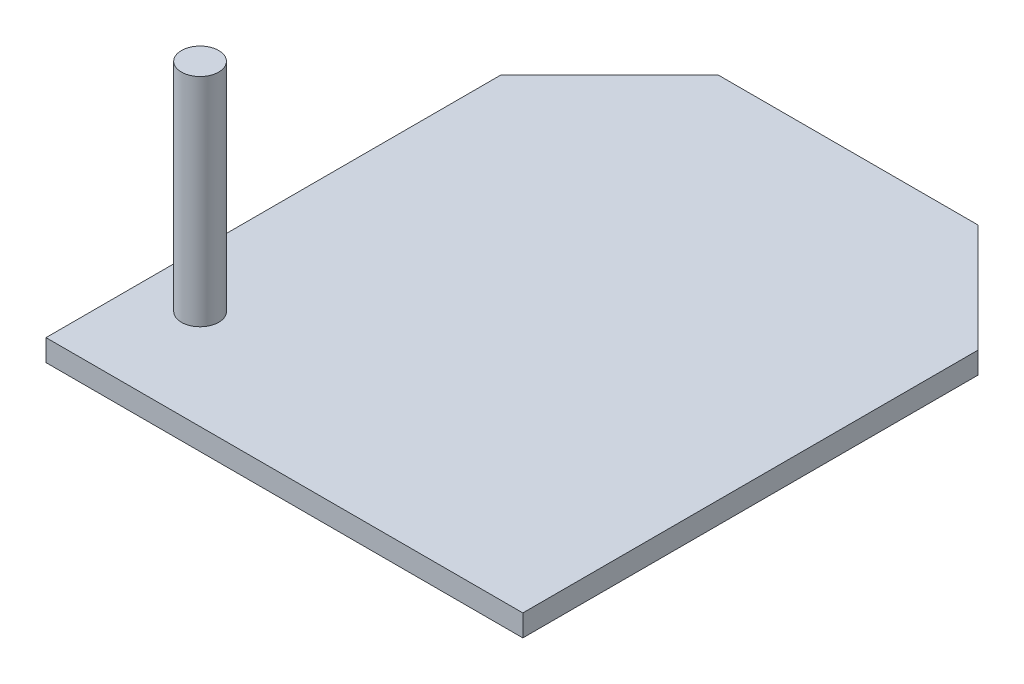
SolidWorks part; units mm, degrees
ref_plane "Front Plane" through (0, 0, 0) normal (0, 0, 1) x (1, 0, 0)
ref_plane "Top Plane" through (0, 0, 0) normal (0, 1, 0) x (1, 0, 0)
ref_plane "Right Plane" through (0, 0, 0) normal (1, 0, 0) x (0, 0, -1)
sketch "Sketch1" plane through (0, 0, 0) normal (0, 1, 0) x (1, 0, 0)
  line L1 (-9.4892, -15.0129) -> (12.5108, -15.0129)
  line L2 (-9.4892, -15.0129) -> (-9.4892, 10.9871)
  line L3 (-9.4892, 10.9871) -> (12.5108, 10.9871)
  line L4 (12.5108, -15.0129) -> (12.5108, 10.9871)
  dimension "D1" = 22
  dimension "D2" = 26
extrude "Extrude1" add sketch "Sketch1" along normal blind 1
chamfer "Chamfer1" distance 5 angle 45 2 edges at (-9.4892, 0.5, -10.9871) (12.5108, 0.5, -10.9871)
sketch "Sketch2" plane through (0, 1, 0) normal (0, 1, 0) x (1, 0, 0)
  circle A0 centre (-6.9757, -10.4177) radius 0.8611
extrude "Extrude2" add sketch "Sketch2" along normal blind 10
